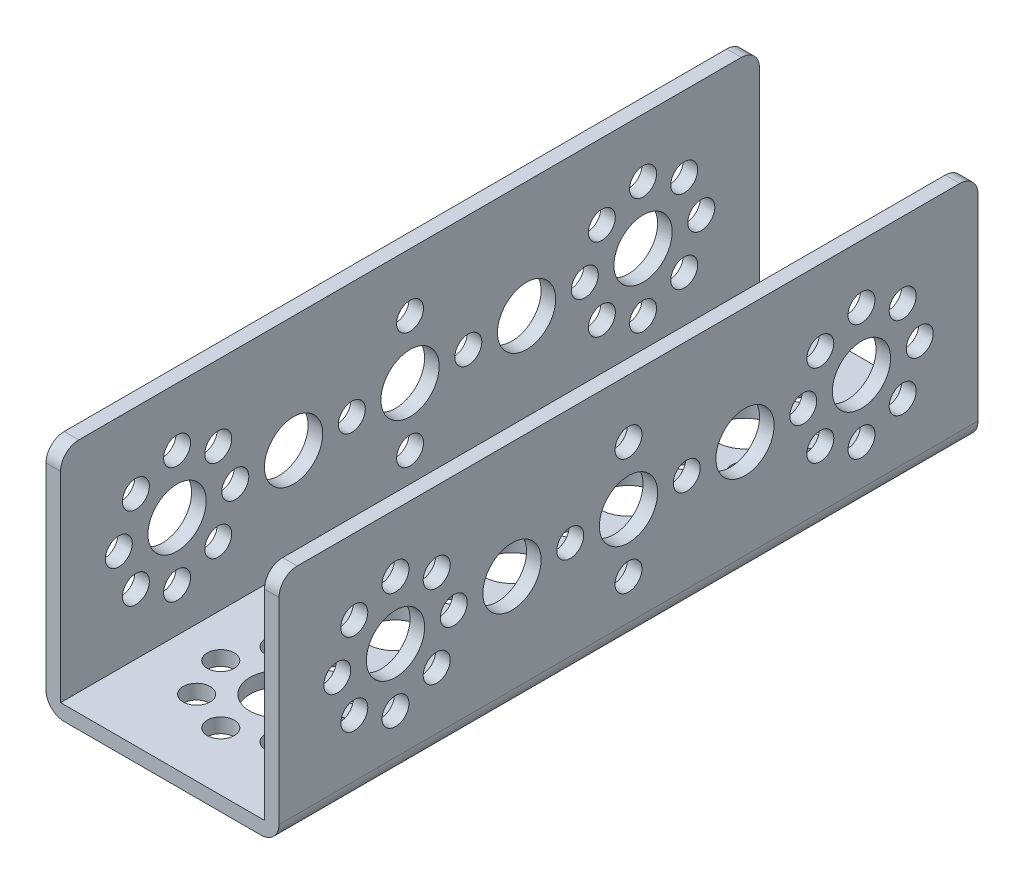
SolidWorks part; units mm, degrees
material "2024 Alloy"
ref_plane "Front Plane" through (0, 0, 0) normal (0, 0, 1) x (1, 0, 0)
ref_plane "Top Plane" through (0, 0, 0) normal (0, 1, 0) x (1, 0, 0)
ref_plane "Right Plane" through (0, 0, 0) normal (1, 0, 0) x (0, 0, -1)
ref_plane "Plane1" through (16, 0, 0) normal (1, 0, 0) x (0, 0, -1)
sketch "Sketch1" plane through (16, 0, 0) normal (1, 0, 0) x (0, 0, -1)
  line L0 (-16, 32) -> (-16, 0)
  line L1 (-16, 0) -> (80, 0)
  line L2 (80, 0) -> (80, 32)
  line L3 (80, 32) -> (-16, 32)
extrude "Boss-Extrude1" add sketch "Sketch1" against normal blind 32
sketch "Sketch2" plane through (0, 0, -80) normal (0, 0, -1) x (-1, 0, 0)
  line L0 (14, 32) -> (-14, 32)
  line L1 (-14, 32) -> (-14, 2)
  line L2 (-14, 2) -> (14, 2)
  line L3 (14, 2) -> (14, 32)
extrude "Cut-Extrude1" cut sketch "Sketch2" against normal through all
hole_wizard "Ø8.0 (8) Diameter Hole1" positions "Sketch4" profile "Sketch3" hole size "Ø8.0" standard "ANSI Metric"
sketch "Sketch4" plane through (-16, 0, 0) normal (-1, 0, 0) x (0, 0, 1)
  point P0 (-64, 16)
  point P1 (-32, 16)
  point P2 (-16, 16)
  point P3 (-48, 16)
  point P4 (0, 16)
sketch "Sketch3" plane through (-16, 16, -64) normal (0, 1, 0) x (0, 0, 1)
  line L0 (0, 0) -> (0, 2)
  line L1 (0, 2) -> (4, 2)
  line L2 (4, 2) -> (4, 0)
  line L5 (4, 0) -> (0, 0)
  line L11 (0, -6.35) -> (0, 107.95) construction
  dimension "Thru Hole Dia." = 8
  dimension "Thru Hole Depth" = 2
hole_wizard "Ø3.7 (3.7) Diameter Hole1" positions "Sketch6" profile "Sketch5" hole size "Ø3.7" standard "ANSI Metric"
sketch "Sketch6" plane through (-16, 0, 0) normal (-1, 0, 0) x (0, 0, 1)
  point P0 (0, 24)
  point P1 (0, 8)
  point P2 (-8, 16)
  point P3 (8, 16)
  point P4 (-5.6569, 21.6569)
  point P5 (5.6569, 21.6569)
  point P6 (5.6569, 10.3431)
  point P7 (-5.6569, 10.3431)
  point P8 (-64, 24)
  point P9 (-64, 8)
  point P10 (-72, 16)
  point P11 (-56, 16)
  point P12 (-69.6569, 21.6569)
  point P13 (-58.3431, 21.6569)
  point P14 (-58.3431, 10.3431)
  point P15 (-69.6569, 10.3431)
  point P16 (-32, 24)
  point P17 (-40, 16)
  point P18 (-32, 8)
  point P19 (-24, 16)
sketch "Sketch5" plane through (-16, 24, 0) normal (0, 1, 0) x (0, 0, 1)
  line L0 (0, 0) -> (0, 2)
  line L1 (0, 2) -> (1.85, 2)
  line L2 (1.85, 2) -> (1.85, 0)
  line L5 (1.85, 0) -> (0, 0)
  line L11 (0, -6.35) -> (0, 107.95) construction
  dimension "Thru Hole Dia." = 3.7
  dimension "Thru Hole Depth" = 2
hole_wizard "Ø3.7 (3.7) Diameter Hole2" positions "Sketch8" profile "Sketch7" hole size "Ø3.7" standard "ANSI Metric"
sketch "Sketch8" plane through (0, 0, 0) normal (0, -1, 0) x (-1, 0, 0)
  point P0 (8, 0)
  point P1 (5.6569, 5.6569)
  point P2 (0, 8)
  point P3 (-5.6569, 5.6569)
  point P4 (-8, 0)
  point P5 (-5.6569, -5.6569)
  point P6 (0, -8)
  point P7 (5.6569, -5.6569)
  point P8 (8, 64)
  point P9 (5.6569, 69.6569)
  point P10 (0, 72)
  point P11 (-5.6569, 69.6569)
  point P12 (-8, 64)
  point P13 (-5.6569, 58.3431)
  point P14 (0, 56)
  point P15 (5.6569, 58.3431)
  point P16 (8, 32)
  point P17 (0, 40)
  point P18 (-8, 32)
  point P19 (0, 24)
sketch "Sketch7" plane through (-8, 0, 0) normal (1, 0, 0) x (0, 0, -1)
  line L0 (0, 0) -> (0, 32)
  line L1 (0, 32) -> (1.85, 32)
  line L2 (1.85, 32) -> (1.85, 0)
  line L5 (1.85, 0) -> (0, 0)
  line L11 (0, -6.35) -> (0, 107.95) construction
  dimension "Thru Hole Dia." = 3.7
  dimension "Thru Hole Depth" = 32
hole_wizard "Ø8.0 (8) Diameter Hole2" positions "Sketch10" profile "Sketch9" hole size "Ø8.0" standard "ANSI Metric"
sketch "Sketch10" plane through (0, 0, 0) normal (0, -1, 0) x (-1, 0, 0)
  point P0 (0, 0)
  point P1 (0, 64)
  point P2 (0, 32)
  point P3 (0, 16)
  point P4 (0, 48)
sketch "Sketch9" plane through (0, 0, 0) normal (1, 0, 0) x (0, 0, -1)
  line L0 (0, 0) -> (0, 32)
  line L1 (0, 32) -> (4, 32)
  line L2 (4, 32) -> (4, 0)
  line L5 (4, 0) -> (0, 0)
  line L11 (0, -6.35) -> (0, 107.95) construction
  dimension "Thru Hole Dia." = 8
  dimension "Thru Hole Depth" = 32
hole_wizard "Ø8.0 (8) Diameter Hole3" positions "Sketch12" profile "Sketch11" hole size "Ø8.0" standard "ANSI Metric"
sketch "Sketch12" plane through (14, 0, 0) normal (-1, 0, 0) x (0, 0, 1)
  point P0 (-32, 16)
sketch "Sketch11" plane through (14, 16, -32) normal (0, 1, 0) x (0, 0, 1)
  line L0 (0, 0) -> (0, 2)
  line L1 (0, 2) -> (4, 2)
  line L2 (4, 2) -> (4, 0)
  line L5 (4, 0) -> (0, 0)
  line L11 (0, -6.35) -> (0, 107.95) construction
  dimension "Thru Hole Dia." = 8
  dimension "Thru Hole Depth" = 2
hole_wizard "Ø8.0 (8) Diameter Hole4" positions "Sketch14" profile "Sketch13" hole size "Ø8.0" standard "ANSI Metric"
sketch "Sketch14" plane through (16, 0, 0) normal (1, 0, 0) x (0, 0, -1)
  point P0 (64, 16)
  point P1 (16, 16)
  point P2 (48, 16)
  point P3 (0, 16)
sketch "Sketch13" plane through (16, 16, -64) normal (0, 1, 0) x (0, 0, -1)
  line L0 (0, 0) -> (0, 32)
  line L1 (0, 32) -> (4, 32)
  line L2 (4, 32) -> (4, 0)
  line L5 (4, 0) -> (0, 0)
  line L11 (0, -6.35) -> (0, 107.95) construction
  dimension "Thru Hole Dia." = 8
  dimension "Thru Hole Depth" = 32
hole_wizard "Ø3.7 (3.7) Diameter Hole3" positions "Sketch16" profile "Sketch15" hole size "Ø3.7" standard "ANSI Metric"
sketch "Sketch16" plane through (16, 0, 0) normal (1, 0, 0) x (0, 0, -1)
  point P0 (0, 24)
  point P1 (0, 8)
  point P2 (8, 16)
  point P3 (-8, 16)
  point P4 (5.6569, 21.6569)
  point P5 (-5.6569, 21.6569)
  point P6 (-5.6569, 10.3431)
  point P7 (5.6569, 10.3431)
  point P8 (64, 24)
  point P9 (64, 8)
  point P10 (72, 16)
  point P11 (56, 16)
  point P12 (69.6569, 21.6569)
  point P13 (58.3431, 21.6569)
  point P14 (58.3431, 10.3431)
  point P15 (69.6569, 10.3431)
  point P16 (32, 24)
  point P17 (40, 16)
  point P18 (32, 8)
  point P19 (24, 16)
sketch "Sketch15" plane through (16, 24, 0) normal (0, 1, 0) x (0, 0, -1)
  line L0 (0, 0) -> (0, 32)
  line L1 (0, 32) -> (1.85, 32)
  line L2 (1.85, 32) -> (1.85, 0)
  line L5 (1.85, 0) -> (0, 0)
  line L11 (0, -6.35) -> (0, 107.95) construction
  dimension "Thru Hole Dia." = 3.7
  dimension "Thru Hole Depth" = 32
fillet "Fillet1" radius 2.5 6 edges at (-16, 0, -32) (-15, 32, -80) (-15, 32, 16) (16, 0, -32) (15, 32, 16) (15, 32, -80)
